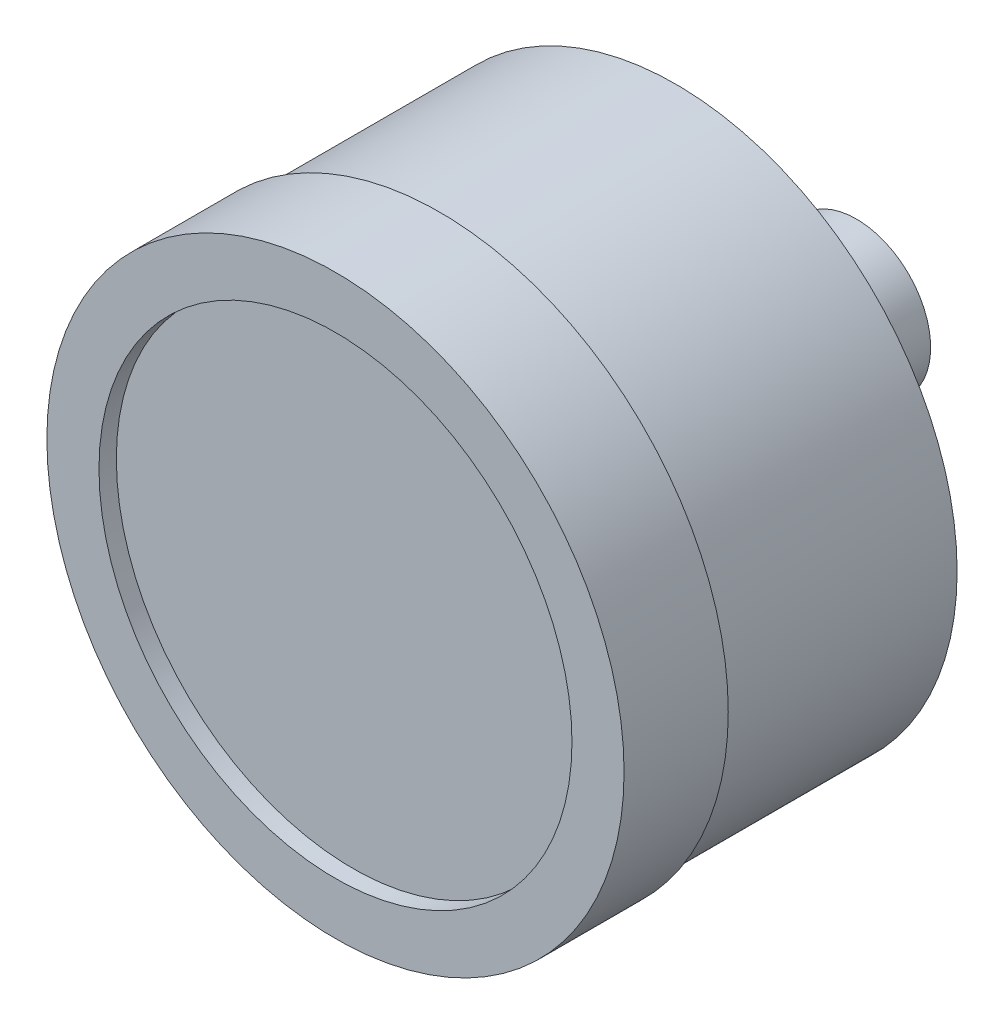
SolidWorks part; units mm, degrees
ref_plane "Front Plane" through (0, 0, 0) normal (0, 0, 1) x (1, 0, 0)
ref_plane "Top Plane" through (0, 0, 0) normal (0, 1, 0) x (1, 0, 0)
ref_plane "Right Plane" through (0, 0, 0) normal (1, 0, 0) x (0, 0, -1)
sketch "Sketch1" plane through (0, 0, 0) normal (0, 0, 1) x (1, 0, 0)
  circle A0 centre (0, 0) radius 20.574
  dimension "D1" = 41.148
extrude "Boss-Extrude1" add sketch "Sketch1" along normal blind 24.892
sketch "Sketch2" plane through (0, 0, 24.892) normal (0, 0, 1) x (1, 0, 0)
  circle A0 centre (0, 0) radius 21.1074
  dimension "D1" = 42.2148
extrude "Boss-Extrude2" add sketch "Sketch2" against normal blind 7.62
sketch "Sketch3" plane through (0, 0, 24.892) normal (0, 0, 1) x (1, 0, 0)
  circle A2 centre (0, 0) radius 17.2974
  circle A3 centre (0, 0) radius 17.2974
  dimension "D1" = 3.81
extrude "Cut-Extrude1" cut sketch "Sketch3" against normal blind 1.27
sketch "Sketch4" plane through (0, 0, 0) normal (0, 0, -1) x (-1, 0, 0)
  line L1 (-5.4293, -5.4292) -> (5.4292, -5.4292)
  line L2 (-5.4293, -5.4292) -> (-5.4293, 5.4292)
  line L3 (-5.4293, 5.4292) -> (5.4292, 5.4292)
  line L4 (5.4292, -5.4292) -> (5.4292, 5.4292)
  line L5 (-5.4293, -5.4292) -> (5.4292, 5.4292) construction
  line L6 (-5.4293, 5.4292) -> (5.4292, -5.4292) construction
  point P0 (0, 0)
  dimension "D1" = 10.8585
extrude "Boss-Extrude3" add sketch "Sketch4" along normal blind 5.715
sketch "Sketch5" plane through (0, 0, -5.715) normal (0, 0, -1) x (-1, 0, 0)
  circle A0 centre (0, 0) radius 5.4292
extrude "Boss-Extrude4" add sketch "Sketch5" along normal blind 7.493
